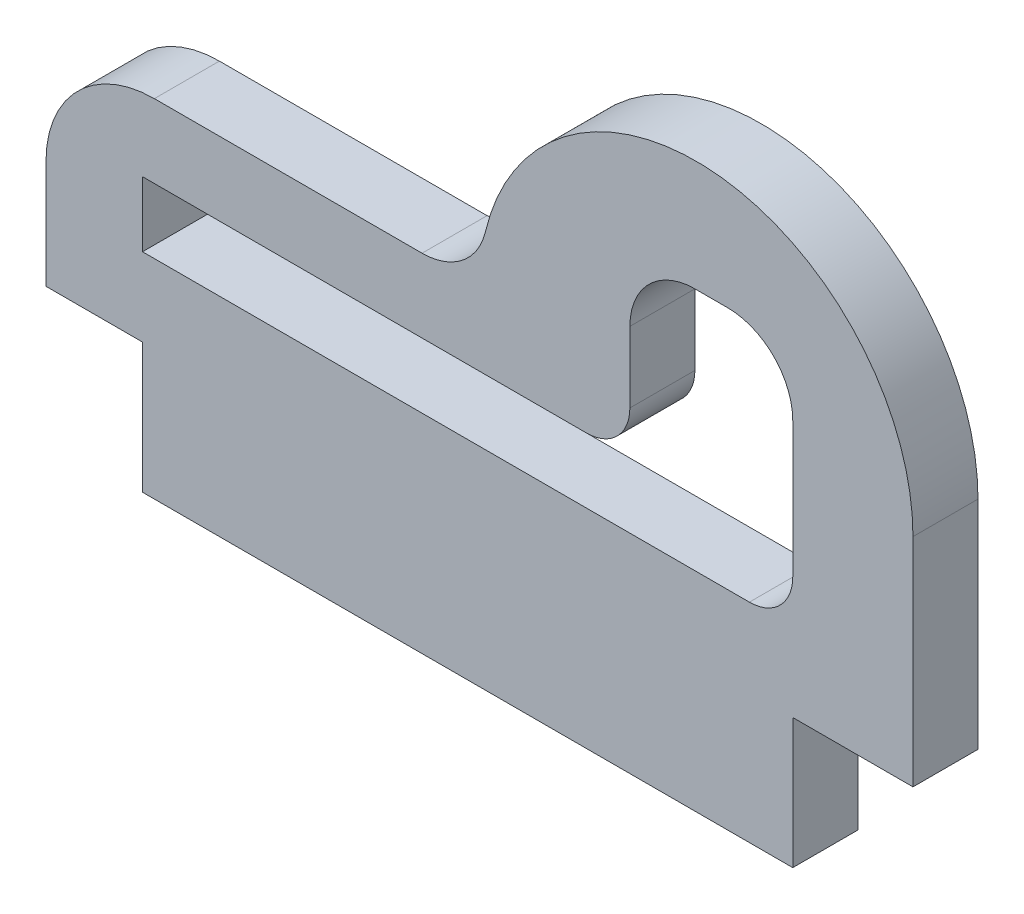
SolidWorks part; units mm, degrees
ref_plane "Alzado" through (0, 0, 0) normal (0, 0, 1) x (1, 0, 0)
ref_plane "Planta" through (0, 0, 0) normal (0, 1, 0) x (1, 0, 0)
ref_plane "Vista lateral" through (0, 0, 0) normal (1, 0, 0) x (0, 0, -1)
sketch "Croquis1" plane through (0, 0, 0) normal (0, 0, 1) x (1, 0, 0)
  line L0 (-2.6491, 0) -> (-15, 0)
  line L1 (-20, -5) -> (-20, -10)
  line L2 (-20, -10) -> (-15.5468, -10)
  line L3 (20, -10) -> (20, 0)
  line L5 (-15.5468, -6.3913) -> (12.4532, -6.3913)
  line L6 (-15.5468, -6.3913) -> (-15.5468, -3.3913)
  line L7 (-15.5468, -3.3913) -> (4.9381, -3.3913)
  line L8 (14.4532, -4.3913) -> (14.4532, -3.3913)
  line L10 (-15.5468, -10) -> (-15.5468, -16)
  line L11 (14.4532, -3.3913) -> (14.4532, 1.8696)
  line L12 (6.9381, -1.3913) -> (6.9381, 1.8696)
  line L13 (11.4532, 4.8696) -> (9.9381, 4.8696)
  line L14 (14.4532, -10) -> (14.4532, -16)
  line L15 (-15.5468, -16) -> (14.4532, -16)
  line L16 (14.4532, -10) -> (20, -10)
  arc A0 (20, 0) -> (0.2699, 2.3077) centre (10, 0) ccw
  arc A1 (-2.6491, 0) -> (0.2699, 2.3077) centre (-2.6491, 3) ccw
  arc A2 (14.4532, 1.8696) -> (11.4532, 4.8696) centre (11.4532, 1.8696) ccw
  arc A3 (6.9381, 1.8696) -> (9.9381, 4.8696) centre (9.9381, 1.8696) cw
  arc A4 (12.4532, -6.3913) -> (14.4532, -4.3913) centre (12.4532, -4.3913) ccw
  arc A5 (4.9381, -3.3913) -> (6.9381, -1.3913) centre (4.9381, -1.3913) ccw
  arc A6 (-15, 0) -> (-20, -5) centre (-15, -5) ccw
  point P7 (-0.5468, -4.8913)
  point P22 (0, 0)
  point P29 (14.4532, -6.3913)
  point P34 (-20, 0)
  dimension "D8" = 3
  dimension "D9" = 2
  dimension "D10" = 5
  dimension "D1" = 40
  dimension "D2" = 10
  dimension "D3" = 20
  dimension "D4" = 10
  dimension "D5" = 3
  dimension "D6" = 30
  dimension "D7" = 6
extrude "Saliente-Extruir1" add sketch "Croquis1" along normal blind 3
